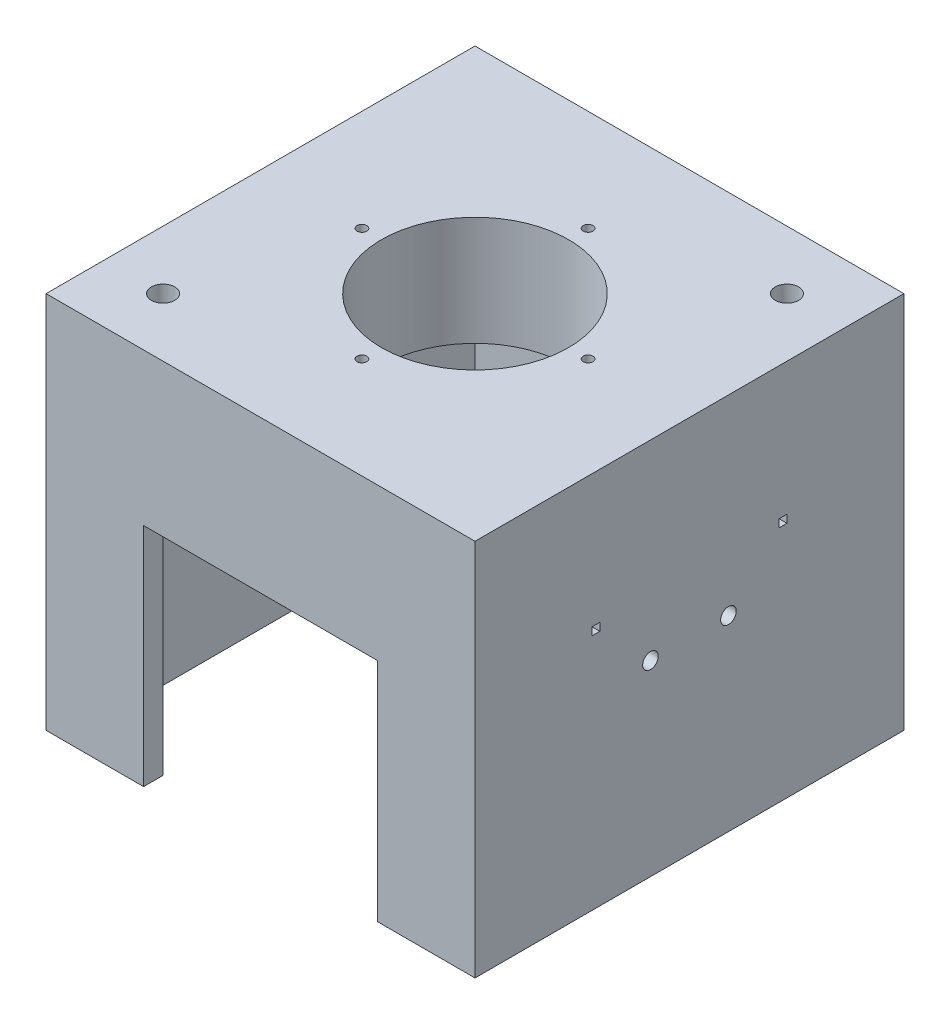
SolidWorks part; units mm, degrees
material "Alloy Steel (SS)"
ref_plane "Front Plane" through (0, 0, 0) normal (0, 0, 1) x (1, 0, 0)
ref_plane "Top Plane" through (0, 0, 0) normal (0, 1, 0) x (1, 0, 0)
ref_plane "Right Plane" through (0, 0, 0) normal (1, 0, 0) x (0, 0, -1)
sketch "Sketch2" plane through (0, 0, 0) normal (0, 1, 0) x (1, 0, 0)
  line L0 (-50, -50) -> (-50, 50)
  line L1 (55, -55) -> (-55, -55)
  line L2 (55, -55) -> (55, 55)
  line L3 (55, 55) -> (-55, 55)
  line L4 (-55, -55) -> (-55, 55)
  line L5 (55, -55) -> (-55, 55) construction
  line L6 (55, 55) -> (-55, -55) construction
  line L7 (50, 50) -> (-50, 50)
  line L8 (50, -50) -> (50, 50)
  line L9 (50, -50) -> (-50, -50)
  point P0 (0, 0)
  dimension "D1" = 110
  dimension "D2" = 110
  dimension "D3" = 5
extrude "Boss-Extrude1" add sketch "Sketch2" along normal blind 89
sketch "Sketch3" plane through (0, 89, 0) normal (0, 1, 0) x (1, 0, 0)
  line L1 (55, -55) -> (-55, -55)
  line L2 (55, -55) -> (55, 55)
  line L3 (55, 55) -> (-55, 55)
  line L4 (-55, -55) -> (-55, 55)
  line L5 (55, -55) -> (-55, 55) construction
  line L6 (55, 55) -> (-55, -55) construction
  point P0 (0, 0)
extrude "Boss-Extrude2" add sketch "Sketch3" along normal blind 8
sketch "Sketch6" plane through (0, 0, 55) normal (0, 0, 1) x (1, 0, 0)
  line L1 (-30, 58) -> (30, 58)
  line L2 (-30, 58) -> (-30, 0)
  line L3 (-30, 0) -> (30, 0)
  line L4 (30, 58) -> (30, 0)
  line L5 (-30, 58) -> (30, 0) construction
  line L6 (-30, 0) -> (30, 58) construction
  point P0 (0, 29)
  point P5 (0, 0)
  dimension "D1" = 58
  dimension "D2" = 60
extrude "Cut-Extrude1" cut sketch "Sketch6" against normal up to next
sketch "Sketch8" plane through (0, 0, 0) normal (0, 0, 1) x (1, 0, 0)
  line L0 (0, 0) -> (0, 97) construction
  line L1 (55, 97) -> (-55, 97) construction
  line L2 (0, 97) -> (-21, 97)
  line L3 (-21, 97) -> (-21, 92.5)
  line L4 (-21, 92.5) -> (-16.2, 92.5)
  line L5 (-16.2, 92.5) -> (-16.2, 88.5)
  line L6 (-16.2, 88.5) -> (0, 88.5)
  line L7 (0, 97) -> (0, 88.5)
  dimension "D1" = 97
  dimension "D2" = 21
  dimension "D3" = 4.5
  dimension "D4" = 4.8
  dimension "D5" = 8.5
  dimension "D6" = 16.2
revolve "Cut-Revolve1" cut sketch "Sketch8" angle 360 about L0
sketch "Sketch9" plane through (0, 58, 0) normal (0, -1, 0) x (1, 0, 0)
  line L1 (55, -55) -> (-55, -55)
  line L2 (55, -55) -> (55, 55)
  line L3 (55, 55) -> (-55, 55)
  line L4 (-55, -55) -> (-55, 55)
  line L5 (55, -55) -> (-55, 55) construction
  line L6 (55, 55) -> (-55, -55) construction
  point P0 (0, 0)
extrude "Boss-Extrude3" add sketch "Sketch9" against normal blind 3
sketch "Sketch10" plane through (0, 61, 0) normal (0, 1, 0) x (1, 0, 0)
  circle A0 centre (0, 0) radius 7.5
  dimension "D1" = 15
extrude "Cut-Extrude2" cut sketch "Sketch10" against normal up to next
sketch "Sketch11" plane through (0, 0, 0) normal (0, 0, 1) x (1, 0, 0)
  line L0 (-50, 89) -> (-35, 89)
  line L1 (50, 89) -> (-50, 89) construction
  line L2 (-35, 89) -> (-50, 69)
  line L3 (-50, 89) -> (-50, 61) construction
  line L4 (-50, 69) -> (-50, 89)
  dimension "D1" = 15
  dimension "D2" = 20
extrude "Boss-Extrude4" add sketch "Sketch11" along normal mid plane 3
mirror "Mirror1" about plane through (0, 0, 0) normal (1, 0, 0) of "Boss-Extrude4"
sketch "Sketch12" plane through (0, 0, 0) normal (1, 0, 0) x (0, 0, -1)
  line L0 (-35, 89) -> (-50, 89)
  line L1 (-1.5, 89) -> (-50, 89) construction
  line L2 (-50, 89) -> (-50, 69)
  line L3 (-50, 89) -> (-50, 61) construction
  line L4 (-50, 69) -> (-35, 89)
  dimension "D1" = 15
  dimension "20" = 20
extrude "Boss-Extrude5" add sketch "Sketch12" along normal mid plane 3
mirror "Mirror2" about plane through (0, 0, 0) normal (0, 0, 1) of "Boss-Extrude5"
sketch "Sketch14" plane through (0, 97, 0) normal (0, 1, 0) x (1, 0, 0)
  line L0 (55, 55) -> (-55, 55) construction
  line L1 (55, -55) -> (55, 55) construction
  line L2 (-55, 55) -> (-55, -55) construction
  line L3 (-55, -55) -> (55, -55) construction
  circle A0 centre (40, 40) radius 3
  circle A1 centre (-40, -40) radius 3
  dimension "D1" = 6
  dimension "D2" = 15
  dimension "D3" = 15
  dimension "D4" = 15
  dimension "D5" = 15
extrude "Cut-Extrude3" cut sketch "Sketch14" against normal blind 73
sketch "Sketch15" plane through (-50, 0, 0) normal (1, 0, 0) x (0, 0, -1)
  line L0 (-50, 61) -> (50, 61) construction
  line L1 (-50, 61) -> (50, 61) construction
  line L2 (0, 61) -> (0, 66.6519) construction
  line L3 (-25, 63) -> (-23, 63)
  line L4 (-25, 63) -> (-25, 61)
  line L5 (-25, 61) -> (-23, 61)
  line L6 (-23, 63) -> (-23, 61)
  line L7 (25, 61) -> (23, 61)
  line L8 (23, 63) -> (23, 61)
  line L9 (25, 63) -> (23, 63)
  line L10 (25, 63) -> (25, 61)
  point P12 (-24, 61)
  dimension "D1" = 2
  dimension "D2" = 2
  dimension "D3" = 25
extrude "Cut-Extrude4" cut sketch "Sketch15" along normal blind 113 and the other way blind 13
sketch "Sketch16" plane through (0, 61, 0) normal (0, 1, 0) x (1, 0, 0)
  line L0 (0, 0) -> (0, 22.115) construction
  circle A0 centre (-13.5, 13.5) radius 2.5
  circle A1 centre (-13.5, -36) radius 2.5
  circle A2 centre (13.5, -36) radius 2.5
  circle A3 centre (13.5, 13.5) radius 2.5
  dimension "D4" = 5
  dimension "D1" = 13.5
  dimension "D2" = 13.5
  dimension "D3" = 36
extrude "Cut-Extrude5" cut sketch "Sketch16" against normal up to next
sketch "Sketch17" plane through (0, 61, 0) normal (0, 1, 0) x (1, 0, 0)
  circle A0 centre (0, 0) radius 11
  circle A1 centre (0, 0) radius 14
  dimension "D1" = 22
  dimension "D2" = 3
extrude "Boss-Extrude6" add sketch "Sketch17" along normal blind 7
sketch "Sketch20" plane through (0, 0, -50) normal (0, 0, 1) x (1, 0, 0)
  line L0 (0, 0) -> (0, 92.5) construction
  line L1 (50, 0) -> (-50, 0) construction
  line L2 (21, 92.5) -> (-21, 92.5) construction
  line L3 (-50, 58) -> (50, 58) construction
  circle A0 centre (10, 48) radius 2
  circle A1 centre (-10, 48) radius 2
  dimension "D1" = 4
  dimension "D2" = 10
  dimension "D3" = 10
extrude "Cut-Extrude8" cut sketch "Sketch20" against normal up to next
sketch "Sketch18" plane through (0, 0, 0) normal (1, 0, 0) x (0, 0, -1)
  line L0 (0, 61) -> (0, 0) construction
  line L1 (7.5, 61) -> (-7.5, 61) construction
  line L2 (50, 58) -> (-50, 58) construction
  circle A0 centre (10, 48) radius 2
  circle A2 centre (-10, 48) radius 2
  dimension "D2" = 10
  dimension "5" = 4
  dimension "D1" = 10
extrude "Cut-Extrude6" cut sketch "Sketch18" against normal mid plane 147
sketch "Sketch19" plane through (0, 61, 0) normal (0, 1, 0) x (1, 0, 0)
  line L0 (0, 0) -> (55, 0) construction
  line L1 (55, -55) -> (55, 55) construction
  line L2 (50, 12) -> (50, 8) construction
  line L3 (0, 0) -> (0, 50) construction
  line L4 (-50, 50) -> (50, 50) construction
  circle A0 centre (40, 10) radius 2
  circle A1 centre (40, -10) radius 2
  circle A2 centre (-40, -10) radius 2
  circle A3 centre (-40, 10) radius 2
  circle A4 centre (10, 40) radius 2
  circle A5 centre (-10, 40) radius 2
  dimension "D3" = 4
  dimension "D6" = 4
  dimension "D1" = 10
  dimension "D2" = 10
  dimension "D4" = 10
  dimension "D5" = 10
extrude "Cut-Extrude7" cut sketch "Sketch19" against normal up to next
sketch "Sketch21" plane through (0, 97, 0) normal (0, 1, 0) x (1, 0, 0)
  circle A0 centre (0, 0) radius 21
  circle A1 centre (0, 0) radius 24
  dimension "D1" = 42
  dimension "D2" = 3
extrude "Boss-Extrude7" add sketch "Sketch21" along normal blind 5
sketch "Sketch22" plane through (0, 0, 0) normal (1, 0, 0) x (0, 0, -1)
  line L0 (0, 97) -> (0, 0) construction
  line L1 (-55, 97) -> (55, 97) construction
  dimension "D1" = 97
sketch "Sketch23" plane through (0, 58, 0) normal (0, -1, 0) x (1, 0, 0)
  line L1 (50, -50) -> (-50, -50)
  line L2 (50, -50) -> (50, 50)
  line L3 (50, 50) -> (-50, 50)
  line L4 (-50, -50) -> (-50, 50)
  line L5 (50, -50) -> (-50, 50) construction
  line L6 (50, 50) -> (-50, -50) construction
  point P0 (0, 0)
extrude "Cut-Extrude9" cut sketch "Sketch23" against normal up to next
sketch "Sketch24" plane through (0, 89, 0) normal (0, -1, 0) x (1, 0, 0)
  line L1 (50, 50) -> (-50, 50)
  line L2 (50, 50) -> (50, -50)
  line L3 (50, -50) -> (-50, -50)
  line L4 (-50, 50) -> (-50, -50)
  line L5 (50, 50) -> (-50, -50) construction
  line L6 (50, -50) -> (-50, 50) construction
  point P0 (0, 0)
extrude "Boss-Extrude8" add sketch "Sketch24" along normal blind 20
sketch "Sketch25" plane through (0, 92.5, 0) normal (0, 1, 0) x (1, 0, 0)
  circle A0 centre (0, 0) radius 24
  dimension "D1" = 48
extrude "Cut-Extrude10" cut sketch "Sketch25" against normal blind 26 and the other way blind 10
sketch "Sketch26" plane through (0, 89, 0) normal (0, 1, 0) x (1, 0, 0)
  circle A0 centre (-40, -40) radius 3
  circle A1 centre (40, 40) radius 3
  dimension "D1" = 6
extrude "Cut-Extrude11" cut sketch "Sketch26" against normal blind 26
sketch "Sketch27" plane through (0, 97, 0) normal (0, 1, 0) x (1, 0, 0)
  circle A0 centre (0, 0) radius 29 construction
  circle A1 centre (0, 29) radius 1.5
  circle A2 centre (29, 0) radius 1.5
  circle A3 centre (0, -29) radius 1.5
  circle A4 centre (-29, 0) radius 1.5
  dimension "D1" = 58
  dimension "D2" = 3
  dimension "D3" = 4
sketch "Sketch29" plane through (0, 69, 0) normal (0, -1, 0) x (1, 0, 0)
  circle A0 centre (0, 0) radius 29 construction
  circle A1 centre (0, 29) radius 1.5
  circle A2 centre (29, 0) radius 1.5
  circle A3 centre (0, -29) radius 1.5
  circle A4 centre (-29, 0) radius 1.5
  dimension "D1" = 58
  dimension "D2" = 3
  dimension "D3" = 4
hole_wizard "M3 Tapped Hole1" positions "3DSketch2" profile "Sketch32" tap size "M3" standard "ISO"
sketch3d "3DSketch2"
  point P0 (-29, 97, 0)
  point P3 (0, 97, 29)
  point P6 (29, 97, 0)
  point P9 (0, 97, -29)
sketch "Sketch32" plane through (-29, 97, 0) normal (1, 0, 0) x (0, 0, 1)
  line L0 (0, 0) -> (0, 7.5)
  line L1 (0, 7.5) -> (1.25, 6.7489)
  line L2 (1.25, 6.7489) -> (1.25, 0)
  line L5 (1.25, 0) -> (0, 0)
  line L10 (0, 7.5) -> (-1.25, 6.7489) construction
  line L11 (0, -6.35) -> (0, 107.95) construction
  dimension "Tap Drill Dia." = 2.5
  dimension "Tap Drill Depth" = 7.5
  dimension "Drill Angle" = 118
cosmetic thread "Hole Thread1" parameters "D1"=6, "D2"=3
cosmetic thread "Hole Thread2" parameters "D1"=6, "D2"=3
cosmetic thread "Hole Thread3" parameters "D1"=6, "D2"=3
cosmetic thread "Hole Thread4" parameters "D1"=6, "D2"=3
hole_wizard "M3 Tapped Hole2" positions "Sketch34" profile "Sketch35" tap size "M3" standard "ISO"
sketch "Sketch34" plane through (0, 69, 0) normal (0, -1, 0) x (-1, 0, 0)
  point P0 (0, -29)
  point P3 (29, 0)
  point P6 (0, 29)
  point P9 (-29, 0)
sketch "Sketch35" plane through (0, 69, 29) normal (1, 0, 0) x (0, 0, -1)
  line L0 (0, 0) -> (0, 7.5)
  line L1 (0, 7.5) -> (1.25, 6.7489)
  line L2 (1.25, 6.7489) -> (1.25, 0)
  line L5 (1.25, 0) -> (0, 0)
  line L10 (0, 7.5) -> (-1.25, 6.7489) construction
  line L11 (0, -6.35) -> (0, 107.95) construction
  dimension "Tap Drill Dia." = 2.5
  dimension "Tap Drill Depth" = 7.5
  dimension "Drill Angle" = 118
cosmetic thread "Hole Thread5" parameters "D1"=6, "D2"=3
cosmetic thread "Hole Thread6" parameters "D1"=6, "D2"=3
cosmetic thread "Hole Thread7" parameters "D1"=6, "D2"=3
cosmetic thread "Hole Thread8" parameters "D1"=6, "D2"=3
